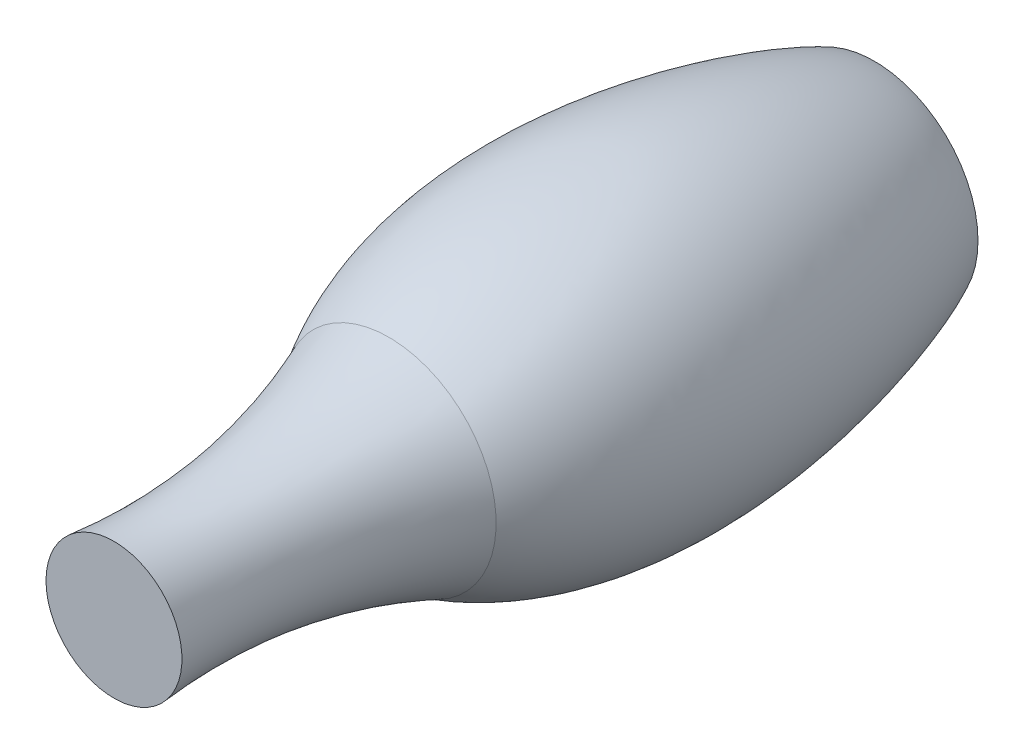
SolidWorks part; units mm, degrees
ref_plane "Front Plane" through (0, 0, 0) normal (0, 0, 1) x (1, 0, 0)
ref_plane "Top Plane" through (0, 0, 0) normal (0, 1, 0) x (1, 0, 0)
ref_plane "Right Plane" through (0, 0, 0) normal (1, 0, 0) x (0, 0, -1)
sketch "Sketch2" plane through (0, 0, 0) normal (0, 1, 0) x (1, 0, 0)
  line L2 (983.9479, -11007.9586) -> (0, -11007.9586)
  line L6 (0, 0) -> (1500, 0)
  line L7 (0, 0) -> (0, -11007.9586)
  spline S0 degree 2 poles (983.9479, -11007.9586) (778.0246, -8933.8565) (1552.785, -7028.3263) knots 0 0 0 1 1 1
  spline S1 degree 3 poles (1500, 0) (1901.1825, -776.854) (3061.4617, -4517.415) (1552.785, -7028.3263) knots 0 0 0 0 1 1 1 1
  dimension "D2" = 1500
revolve "Revolve4" add sketch "Sketch2" angle 360 about L7
sketch "Sketch4" plane through (0, 0, 0) normal (0, 0, -1) x (-1, 0, 0)
  line L0 (0, 1250) -> (0, -1250) construction
  circle A3 centre (0, 0) radius 1250
  circle A4 centre (0, 0) radius 1250
  point P3 (0, 1250)
  point P7 (0, 0)
  point P8 (0, 0)
  point P9 (0, -1250)
  dimension "D1" = 250
sketch "Sketch5" plane through (0, 0, 0) normal (0, 0, -1) x (-1, 0, 0)
  line L0 (0, -1250) -> (0, 1250) construction
  circle A0 centre (0, 0) radius 1250
extrude "Cut-Extrude2" cut sketch "Sketch5" against normal blind 250
sketch "Sketch6" plane through (0, 0, 0) normal (0, 0, -1) x (-1, 0, 0)
  line L0 (0, -1250) -> (0, 1250) construction
  line L1 (1250, 0) -> (-1250, 0) construction
  circle A0 centre (0, 0) radius 1250 construction
sketch "Sketch8" plane through (0, 0, 250) normal (0, 0, -1) x (-1, 0, 0)
  circle A1 centre (800.5545, 0) radius 300
  circle A2 centre (400.2773, -693.3006) radius 300
  circle A3 centre (-400.2773, -693.3006) radius 300
  circle A4 centre (-800.5545, 0) radius 300
  circle A5 centre (-400.2773, 693.3006) radius 300
  circle A6 centre (400.2773, 693.3006) radius 300
  dimension "D1" = 600
  dimension "D2" = 600
  dimension "D3" = 600
  dimension "D4" = 600
  dimension "D5" = 600
  dimension "D6" = 600
extrude "Cut-Extrude5" cut sketch "Sketch8" against normal blind 250
